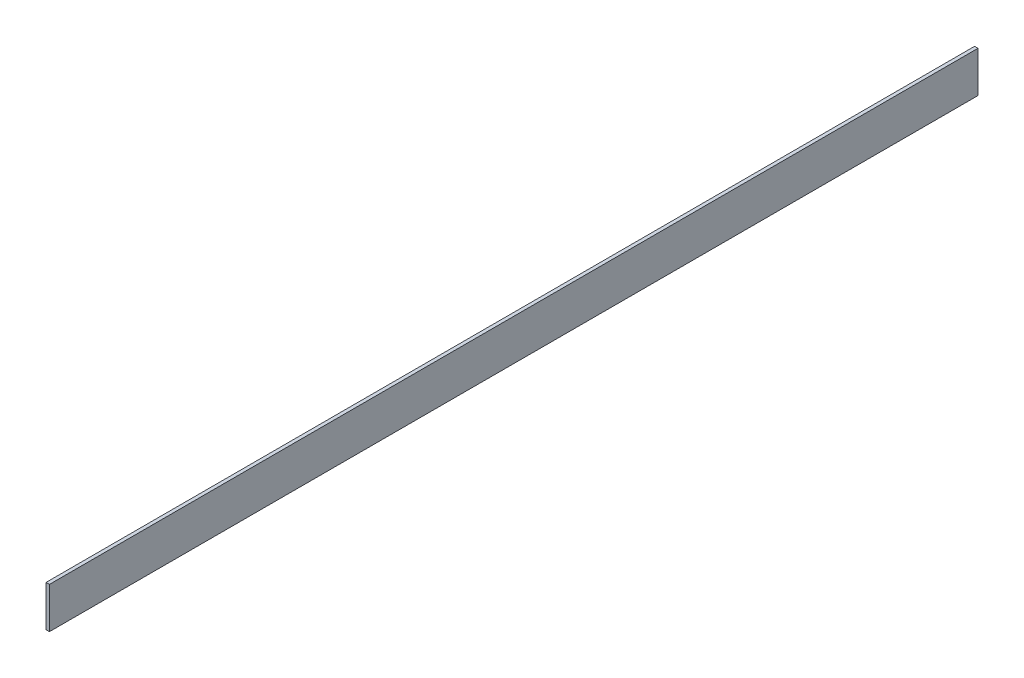
SolidWorks part; units mm, degrees
ref_plane "Front Plane" through (0, 0, 0) normal (0, 0, 1) x (1, 0, 0)
ref_plane "Top Plane" through (0, 0, 0) normal (0, 1, 0) x (1, 0, 0)
ref_plane "Right Plane" through (0, 0, 0) normal (1, 0, 0) x (0, 0, -1)
sketch "Sketch1" plane through (0, 0, 0) normal (0, 1, 0) x (1, 0, 0)
  line L1 (0, 0) -> (3.175, 0)
  line L2 (0, 0) -> (0, 863.6)
  line L3 (0, 863.6) -> (3.175, 863.6)
  line L4 (3.175, 0) -> (3.175, 863.6)
  dimension "D1" = 863.6
  dimension "D2" = 3.175
extrude "Boss-Extrude1" add sketch "Sketch1" along normal blind 38.1
